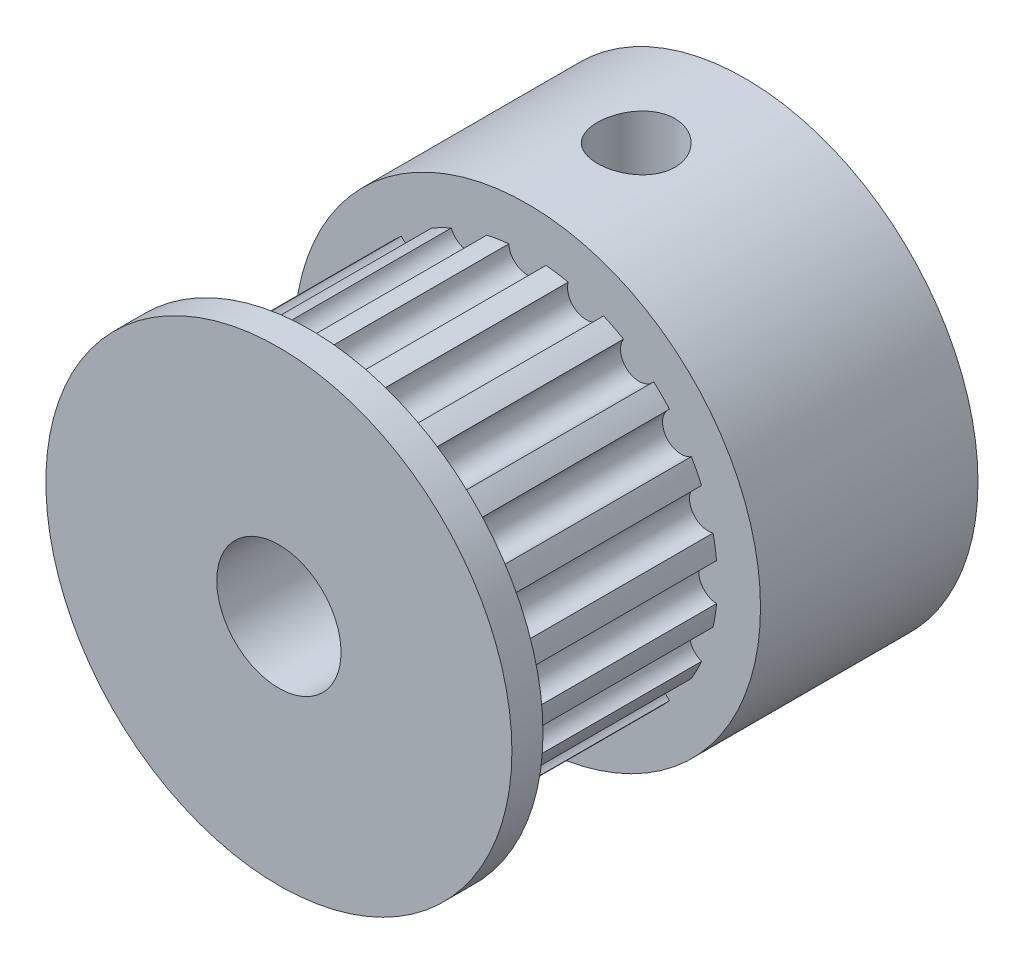
SolidWorks part; units mm, degrees
material "6061 合金"
ref_plane "前基準面" through (0, 0, 0) normal (0, 0, 1) x (1, 0, 0)
ref_plane "上基準面" through (0, 0, 0) normal (0, 1, 0) x (1, 0, 0)
ref_plane "右基準面" through (0, 0, 0) normal (1, 0, 0) x (0, 0, -1)
sketch "草圖1" plane through (0, 0, 0) normal (0, 0, 1) x (1, 0, 0)
  circle A0 centre (0, 0) radius 7.5
  dimension "D1" = 15
extrude "填料-伸長1" add sketch "草圖1" along normal mid plane 7
sketch "草圖2" plane through (0, 0, 3.5) normal (0, 0, 1) x (1, 0, 0)
  circle A0 centre (0, 0) radius 6.115
  dimension "D1" = 12.23
extrude "填料-伸長2" add sketch "草圖2" along normal blind 7
sketch "草圖7" plane through (0, 0, 10.5) normal (0, 0, 1) x (1, 0, 0)
  line L0 (0, 0) -> (0, 6.115) construction
  arc A0 (-0.5993, 6.0856) -> (0.5993, 6.0856) centre (0, 6.115) ccw
  circle A1 centre (0, 0) radius 6.115 construction
  circle A2 centre (0, 0) radius 6.115 construction
  arc A3 (-0.5993, 6.0856) -> (0.5993, 6.0856) centre (0, 0) cw
  point P10 (0, 5.515)
  dimension "D1" = 0.6
extrude "除料-伸長3" cut sketch "草圖7" against normal up to surface (7 mm away) up to face at (6.115, 0, 3.5)
sketch "草圖3" plane through (0, 0, 10.5) normal (0, 0, 1) x (1, 0, 0)
  circle A0 centre (0, 0) radius 7.5
  circle A1 centre (0, 0) radius 7.5 construction
extrude "填料-伸長3" add sketch "草圖3" along normal blind 1
sketch "草圖6" plane through (0, 0, -3.5) normal (0, 0, -1) x (-1, 0, 0)
  circle A0 centre (0, 0) radius 2
  dimension "D1" = 4
extrude "除料-伸長2" cut sketch "草圖6" against normal through all
pattern_circular "環狀複製排列2" count 20 over 360 about axis through (0, 0, 0) along (0, 0, 1) of "除料-伸長3"
hole_wizard "M3x0.5 螺紋孔3" positions "草圖12" profile "草圖13" tap size "M3x0.5" standard "Ansi Metric"
sketch "草圖12" plane through (0, 0, 0) normal (0, 1, 0) x (1, 0, 0)
  point P0 (0, 0)
sketch "草圖13" plane through (0, 0, 0) normal (1, 0, 0) x (0, 0, -1)
  line L0 (0, 0) -> (0, 7.5)
  line L1 (0, 7.5) -> (1.25, 7.5)
  line L2 (1.25, 7.5) -> (1.25, 0)
  line L5 (1.25, 0) -> (0, 0)
  line L11 (0, -6.35) -> (0, 107.95) construction
  dimension "貫穿螺孔鑽直徑" = 2.5
  dimension "貫穿螺孔鑽深度" = 7.5
pattern_circular "環狀複製排列4" count 2 over 90 about axis through (0, 0, 3.5) along (0, 0, -1) of "M3x0.5 螺紋孔3"
